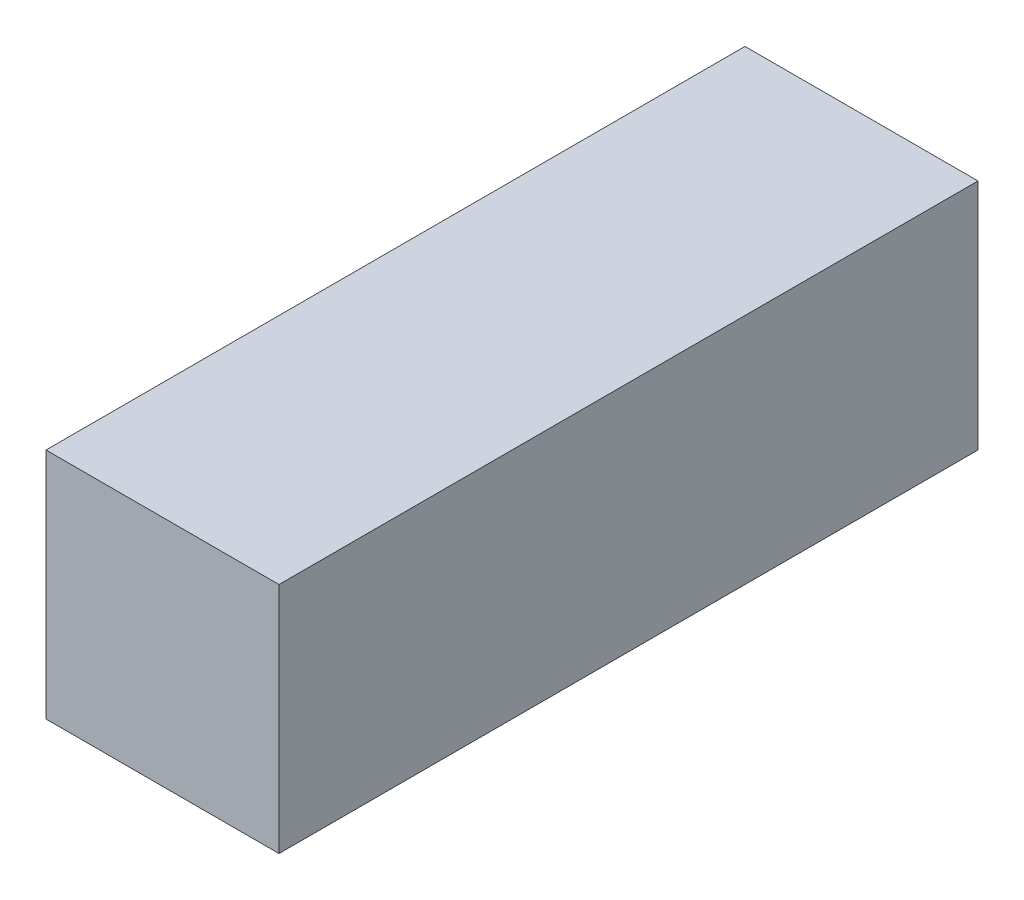
SolidWorks part; units mm, degrees
ref_plane "Front Plane" through (0, 0, 0) normal (0, 0, 1) x (1, 0, 0)
ref_plane "Top Plane" through (0, 0, 0) normal (0, 1, 0) x (1, 0, 0)
ref_plane "Right Plane" through (0, 0, 0) normal (1, 0, 0) x (0, 0, -1)
sketch "Sketch1" plane through (0, 0, 0) normal (0, 1, 0) x (1, 0, 0)
  line L1 (-5, 15) -> (5, 15)
  line L2 (-5, 15) -> (-5, -15)
  line L3 (-5, -15) -> (5, -15)
  line L4 (5, 15) -> (5, -15)
  line L5 (-5, 15) -> (5, -15) construction
  line L6 (-5, -15) -> (5, 15) construction
  point P0 (0, 0)
  dimension "D1" = 10
  dimension "D2" = 30
extrude "Boss-Extrude1" add sketch "Sketch1" along normal blind 10
